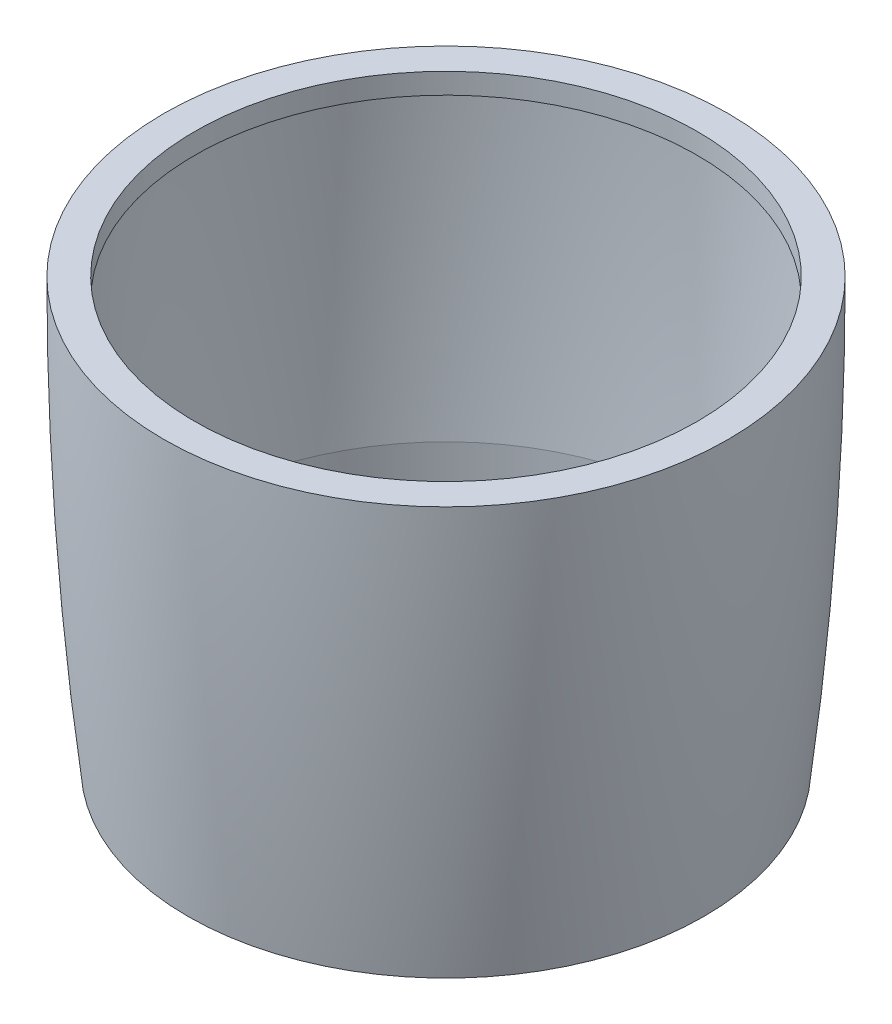
SolidWorks part; units mm, degrees
material "ABS"
ref_plane "Front Plane" through (0, 0, 0) normal (0, 0, 1) x (1, 0, 0)
ref_plane "Top Plane" through (0, 0, 0) normal (0, 1, 0) x (1, 0, 0)
ref_plane "Right Plane" through (0, 0, 0) normal (1, 0, 0) x (0, 0, -1)
sketch "Sketch1" plane through (0, 0, 0) normal (0, 0, 1) x (1, 0, 0)
  line L0 (0, -1072.8003) -> (0, 52567.2128) construction
  line L1 (-20.5, 0) -> (-18.25, 0)
  line L2 (-18.25, 0) -> (-18.25, -1.5)
  line L3 (-18.25, -30.8813) -> (-18.75, -30.8813)
  line L4 (-18.25, -30.8813) -> (-18.25, -35) construction
  line L5 (-18.25, -1.5) -> (-19.2459, -1.5)
  line L6 (-18.25, -1.5) -> (-18.25, -23.3065) construction
  line L7 (-18.25, -23.3065) -> (-18.25, -30.8813)
  arc A0 (-20.5, 0) -> (-18.75, -30.8813) centre (252.8472, 0) ccw
  arc A1 (-18.75, -30.8813) -> (-18.25, -35) centre (252.8472, 0) ccw construction
  arc A2 (-19.2459, -1.5) -> (-18.25, -23.3065) centre (252.8472, 0) ccw
  dimension "D6" = 1.25
  dimension "D1" = 41
  dimension "D2" = 36.5
  dimension "D3" = 35
  dimension "D4" = 0.5
  dimension "D5" = 1.5
revolve "Revolve1" add sketch "Sketch1" angle 360 about L0
